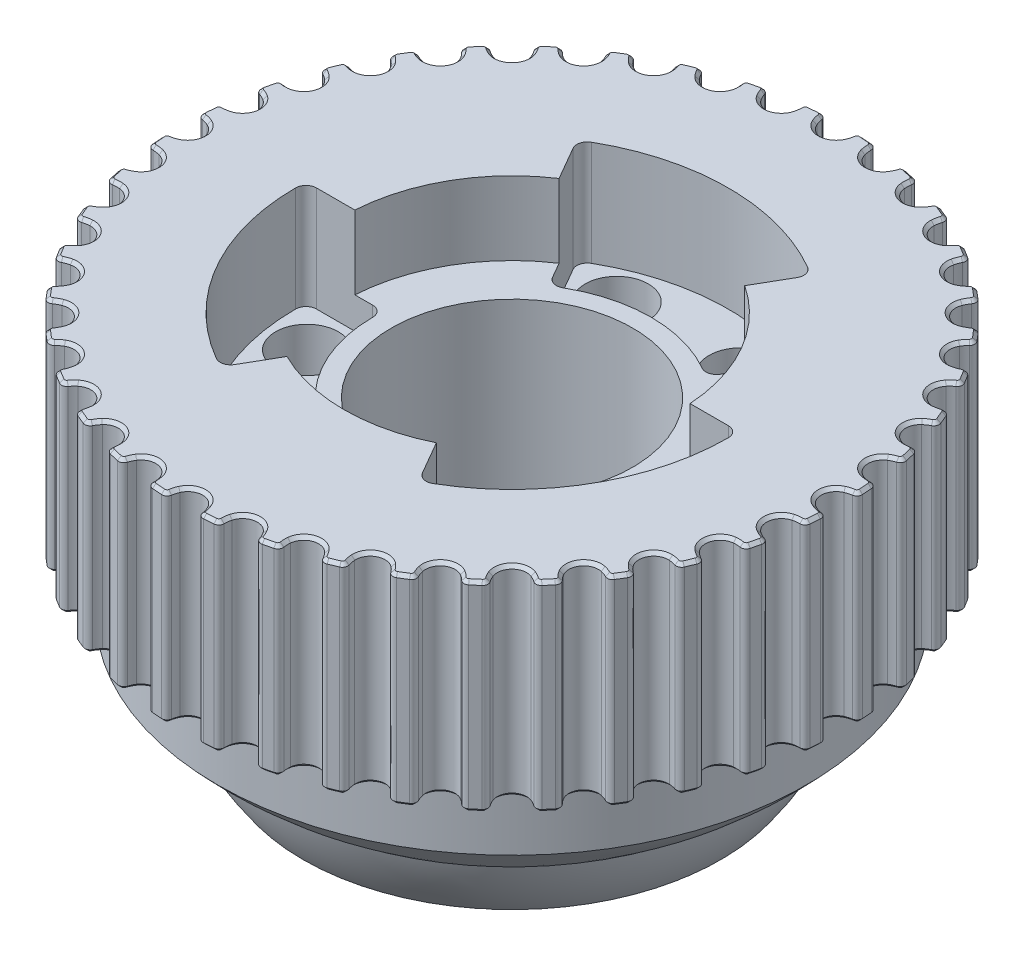
SolidWorks part; units mm, degrees
ref_plane "Front Plane" through (0, 0, 0) normal (0, 0, 1) x (1, 0, 0)
ref_plane "Top Plane" through (0, 0, 0) normal (0, 1, 0) x (1, 0, 0)
ref_plane "Right Plane" through (0, 0, 0) normal (1, 0, 0) x (0, 0, -1)
sketch "Sketch1" plane through (0, 0, 0) normal (0, 1, 0) x (1, 0, 0)
  line L0 (-2.9194, 31.3274) -> (-2.0172, 31.3984)
  line L1 (0, 0) -> (0, 30.8888) construction
  line L2 (0, 0) -> (-4.8321, 30.5085) construction
  line L3 (2.0172, 31.3984) -> (2.9194, 31.3274)
  line L4 (6.9042, 30.6963) -> (7.7841, 30.485)
  line L5 (11.6211, 29.2383) -> (12.4572, 28.892)
  line L6 (16.0519, 27.0604) -> (16.8235, 26.5875)
  line L7 (20.0875, 24.2161) -> (20.7756, 23.6284)
  line L8 (23.6284, 20.7756) -> (24.2161, 20.0875)
  line L9 (26.5875, 16.8235) -> (27.0604, 16.0519)
  line L10 (28.892, 12.4572) -> (29.2383, 11.6211)
  line L11 (30.485, 7.7841) -> (30.6963, 6.9042)
  line L12 (31.3274, 2.9194) -> (31.3984, 2.0172)
  line L13 (31.3984, -2.0172) -> (31.3274, -2.9194)
  line L14 (30.6963, -6.9042) -> (30.485, -7.7841)
  line L15 (29.2383, -11.6211) -> (28.892, -12.4572)
  line L16 (27.0604, -16.0519) -> (26.5875, -16.8235)
  line L17 (24.2161, -20.0875) -> (23.6284, -20.7756)
  line L18 (20.7756, -23.6284) -> (20.0875, -24.2161)
  line L19 (16.8235, -26.5875) -> (16.0519, -27.0604)
  line L20 (12.4572, -28.892) -> (11.6211, -29.2383)
  line L21 (7.7841, -30.485) -> (6.9042, -30.6963)
  line L22 (2.9194, -31.3274) -> (2.0172, -31.3984)
  line L23 (-2.0172, -31.3984) -> (-2.9194, -31.3274)
  line L24 (-6.9042, -30.6963) -> (-7.7841, -30.485)
  line L25 (-11.6211, -29.2383) -> (-12.4572, -28.892)
  line L26 (-16.0519, -27.0604) -> (-16.8235, -26.5875)
  line L27 (-20.0875, -24.2161) -> (-20.7756, -23.6284)
  line L28 (-23.6284, -20.7756) -> (-24.2161, -20.0875)
  line L29 (-26.5875, -16.8235) -> (-27.0604, -16.0519)
  line L30 (-28.892, -12.4572) -> (-29.2383, -11.6211)
  line L31 (-30.485, -7.7841) -> (-30.6963, -6.9042)
  line L32 (-31.3274, -2.9194) -> (-31.3984, -2.0172)
  line L33 (-31.3984, 2.0172) -> (-31.3274, 2.9194)
  line L34 (-30.6963, 6.9042) -> (-30.485, 7.7841)
  line L35 (-29.2383, 11.6211) -> (-28.892, 12.4572)
  line L36 (-27.0604, 16.0519) -> (-26.5875, 16.8235)
  line L37 (-24.2161, 20.0875) -> (-23.6284, 20.7756)
  line L38 (-20.7756, 23.6284) -> (-20.0875, 24.2161)
  line L39 (-16.8235, 26.5875) -> (-16.0519, 27.0604)
  line L40 (-12.4572, 28.892) -> (-11.6211, 29.2383)
  line L41 (-7.7841, 30.485) -> (-6.9042, 30.6963)
  line L42 (0, 0) -> (1.2885, 30.3296) construction
  arc A0 (-2.0172, 31.3984) -> (-1.4757, 30.9718) centre (-1.9774, 30.892) cw
  arc A1 (-1.4757, 30.9718) -> (-1.2885, 30.3296) centre (1.1557, 31.3903) ccw
  arc A2 (-1.2885, 30.3296) -> (1.2885, 30.3296) centre (0, 30.8888) ccw
  arc A3 (1.4757, 30.9718) -> (1.2885, 30.3296) centre (-1.1557, 31.3903) cw
  arc A4 (2.0172, 31.3984) -> (1.4757, 30.9718) centre (1.9774, 30.892) ccw
  arc A5 (0, 30.8888) -> (-4.8321, 30.5085) centre (0, 0) ccw construction
  arc A6 (2.9194, 31.3274) -> (3.3875, 30.8213) centre (2.8795, 30.821) cw
  arc A7 (3.3875, 30.8213) -> (3.4719, 30.1578) centre (6.052, 30.8231) ccw
  arc A8 (3.4719, 30.1578) -> (6.0172, 29.7546) centre (4.8321, 30.5085) ccw
  arc A9 (6.3026, 30.3596) -> (6.0172, 29.7546) centre (3.7691, 31.1847) cw
  arc A10 (6.9042, 30.6963) -> (6.3026, 30.3596) centre (6.7856, 30.2023) ccw
  arc A11 (7.7841, 30.485) -> (8.1674, 29.9119) centre (7.6656, 29.9911) cw
  arc A12 (8.1674, 29.9119) -> (8.1469, 29.2433) centre (10.7993, 29.4969) ccw
  arc A13 (8.1469, 29.2433) -> (10.5978, 28.447) centre (9.5452, 29.377) ccw
  arc A14 (10.9743, 28.9999) -> (10.5978, 28.447) centre (8.601, 30.2111) cw
  arc A15 (11.6211, 29.2383) -> (10.9743, 28.9999) centre (11.4267, 28.769) ccw
  arc A16 (12.4572, 28.892) -> (12.7461, 28.266) centre (12.2628, 28.4227) cw
  arc A17 (12.7461, 28.266) -> (12.6213, 27.6088) centre (15.2807, 27.4443) ccw
  arc A18 (12.6213, 27.6088) -> (14.9174, 26.4389) centre (14.0232, 27.5221) ccw
  arc A19 (15.3757, 26.9261) -> (14.9174, 26.4389) centre (13.2212, 28.4937) cw
  arc A20 (16.0519, 27.0604) -> (15.3757, 26.9261) centre (15.7865, 26.6272) ccw
  arc A21 (16.8235, 26.5875) -> (17.0109, 25.9241) centre (16.5581, 26.1544) cw
  arc A22 (17.0109, 25.9241) -> (16.7849, 25.2945) centre (19.3858, 24.716) ccw
  arc A23 (16.7849, 25.2945) -> (18.8697, 23.7798) centre (18.156, 24.9896) ccw
  arc A24 (19.3986, 24.1893) -> (18.8697, 23.7798) centre (17.5158, 26.0746) cw
  arc A25 (20.0875, 24.2161) -> (19.3986, 24.1893) centre (19.7576, 23.8299) ccw
  arc A26 (20.7756, 23.6284) -> (20.8569, 22.9438) centre (20.4457, 23.2421) cw
  arc A27 (20.8569, 22.9438) -> (20.5352, 22.3574) centre (23.0135, 21.3791) ccw
  arc A28 (20.5352, 22.3574) -> (22.3574, 20.5352) centre (21.8417, 21.8417) ccw
  arc A29 (22.9438, 20.8569) -> (22.3574, 20.5352) centre (21.3791, 23.0135) cw
  arc A30 (23.6284, 20.7756) -> (22.9438, 20.8569) centre (23.2421, 20.4457) ccw
  arc A31 (24.2161, 20.0875) -> (24.1893, 19.3986) centre (23.8299, 19.7576) cw
  arc A32 (24.1893, 19.3986) -> (23.7798, 18.8697) centre (26.0746, 17.5158) ccw
  arc A33 (23.7798, 18.8697) -> (25.2945, 16.7849) centre (24.9896, 18.156) ccw
  arc A34 (25.9241, 17.0109) -> (25.2945, 16.7849) centre (24.716, 19.3858) cw
  arc A35 (26.5875, 16.8235) -> (25.9241, 17.0109) centre (26.1544, 16.5581) ccw
  arc A36 (27.0604, 16.0519) -> (26.9261, 15.3757) centre (26.6272, 15.7865) cw
  arc A37 (26.9261, 15.3757) -> (26.4389, 14.9174) centre (28.4937, 13.2212) ccw
  arc A38 (26.4389, 14.9174) -> (27.6088, 12.6213) centre (27.5221, 14.0232) ccw
  arc A39 (28.266, 12.7461) -> (27.6088, 12.6213) centre (27.4443, 15.2807) cw
  arc A40 (28.892, 12.4572) -> (28.266, 12.7461) centre (28.4227, 12.2628) ccw
  arc A41 (29.2383, 11.6211) -> (28.9999, 10.9743) centre (28.769, 11.4267) cw
  arc A42 (28.9999, 10.9743) -> (28.447, 10.5978) centre (30.2111, 8.601) ccw
  arc A43 (28.447, 10.5978) -> (29.2433, 8.1469) centre (29.377, 9.5452) ccw
  arc A44 (29.9119, 8.1674) -> (29.2433, 8.1469) centre (29.4969, 10.7993) cw
  arc A45 (30.485, 7.7841) -> (29.9119, 8.1674) centre (29.9911, 7.6656) ccw
  arc A46 (30.6963, 6.9042) -> (30.3596, 6.3026) centre (30.2023, 6.7856) cw
  arc A47 (30.3596, 6.3026) -> (29.7546, 6.0172) centre (31.1847, 3.7691) ccw
  arc A48 (29.7546, 6.0172) -> (30.1578, 3.4719) centre (30.5085, 4.8321) ccw
  arc A49 (30.8213, 3.3875) -> (30.1578, 3.4719) centre (30.8231, 6.052) cw
  arc A50 (31.3274, 2.9194) -> (30.8213, 3.3875) centre (30.821, 2.8795) ccw
  arc A51 (31.3984, 2.0172) -> (30.9718, 1.4757) centre (30.892, 1.9774) cw
  arc A52 (30.9718, 1.4757) -> (30.3296, 1.2885) centre (31.3903, -1.1557) ccw
  arc A53 (30.3296, 1.2885) -> (30.3296, -1.2885) centre (30.8888, 0) ccw
  arc A54 (30.9718, -1.4757) -> (30.3296, -1.2885) centre (31.3903, 1.1557) cw
  arc A55 (31.3984, -2.0172) -> (30.9718, -1.4757) centre (30.892, -1.9774) ccw
  arc A56 (31.3274, -2.9194) -> (30.8213, -3.3875) centre (30.821, -2.8795) cw
  arc A57 (30.8213, -3.3875) -> (30.1578, -3.4719) centre (30.8231, -6.052) ccw
  arc A58 (30.1578, -3.4719) -> (29.7546, -6.0172) centre (30.5085, -4.8321) ccw
  arc A59 (30.3596, -6.3026) -> (29.7546, -6.0172) centre (31.1847, -3.7691) cw
  arc A60 (30.6963, -6.9042) -> (30.3596, -6.3026) centre (30.2023, -6.7856) ccw
  arc A61 (30.485, -7.7841) -> (29.9119, -8.1674) centre (29.9911, -7.6656) cw
  arc A62 (29.9119, -8.1674) -> (29.2433, -8.1469) centre (29.4969, -10.7993) ccw
  arc A63 (29.2433, -8.1469) -> (28.447, -10.5978) centre (29.377, -9.5452) ccw
  arc A64 (28.9999, -10.9743) -> (28.447, -10.5978) centre (30.2111, -8.601) cw
  arc A65 (29.2383, -11.6211) -> (28.9999, -10.9743) centre (28.769, -11.4267) ccw
  arc A66 (28.892, -12.4572) -> (28.266, -12.7461) centre (28.4227, -12.2628) cw
  arc A67 (28.266, -12.7461) -> (27.6088, -12.6213) centre (27.4443, -15.2807) ccw
  arc A68 (27.6088, -12.6213) -> (26.4389, -14.9174) centre (27.5221, -14.0232) ccw
  arc A69 (26.9261, -15.3757) -> (26.4389, -14.9174) centre (28.4937, -13.2212) cw
  arc A70 (27.0604, -16.0519) -> (26.9261, -15.3757) centre (26.6272, -15.7865) ccw
  arc A71 (26.5875, -16.8235) -> (25.9241, -17.0109) centre (26.1544, -16.5581) cw
  arc A72 (25.9241, -17.0109) -> (25.2945, -16.7849) centre (24.716, -19.3858) ccw
  arc A73 (25.2945, -16.7849) -> (23.7798, -18.8697) centre (24.9896, -18.156) ccw
  arc A74 (24.1893, -19.3986) -> (23.7798, -18.8697) centre (26.0746, -17.5158) cw
  arc A75 (24.2161, -20.0875) -> (24.1893, -19.3986) centre (23.8299, -19.7576) ccw
  arc A76 (23.6284, -20.7756) -> (22.9438, -20.8569) centre (23.2421, -20.4457) cw
  arc A77 (22.9438, -20.8569) -> (22.3574, -20.5352) centre (21.3791, -23.0135) ccw
  arc A78 (22.3574, -20.5352) -> (20.5352, -22.3574) centre (21.8417, -21.8417) ccw
  arc A79 (20.8569, -22.9438) -> (20.5352, -22.3574) centre (23.0135, -21.3791) cw
  arc A80 (20.7756, -23.6284) -> (20.8569, -22.9438) centre (20.4457, -23.2421) ccw
  arc A81 (20.0875, -24.2161) -> (19.3986, -24.1893) centre (19.7576, -23.8299) cw
  arc A82 (19.3986, -24.1893) -> (18.8697, -23.7798) centre (17.5158, -26.0746) ccw
  arc A83 (18.8697, -23.7798) -> (16.7849, -25.2945) centre (18.156, -24.9896) ccw
  arc A84 (17.0109, -25.9241) -> (16.7849, -25.2945) centre (19.3858, -24.716) cw
  arc A85 (16.8235, -26.5875) -> (17.0109, -25.9241) centre (16.5581, -26.1544) ccw
  arc A86 (16.0519, -27.0604) -> (15.3757, -26.9261) centre (15.7865, -26.6272) cw
  arc A87 (15.3757, -26.9261) -> (14.9174, -26.4389) centre (13.2212, -28.4937) ccw
  arc A88 (14.9174, -26.4389) -> (12.6213, -27.6088) centre (14.0232, -27.5221) ccw
  arc A89 (12.7461, -28.266) -> (12.6213, -27.6088) centre (15.2807, -27.4443) cw
  arc A90 (12.4572, -28.892) -> (12.7461, -28.266) centre (12.2628, -28.4227) ccw
  arc A91 (11.6211, -29.2383) -> (10.9743, -28.9999) centre (11.4267, -28.769) cw
  arc A92 (10.9743, -28.9999) -> (10.5978, -28.447) centre (8.601, -30.2111) ccw
  arc A93 (10.5978, -28.447) -> (8.1469, -29.2433) centre (9.5452, -29.377) ccw
  arc A94 (8.1674, -29.9119) -> (8.1469, -29.2433) centre (10.7993, -29.4969) cw
  arc A95 (7.7841, -30.485) -> (8.1674, -29.9119) centre (7.6656, -29.9911) ccw
  arc A96 (6.9042, -30.6963) -> (6.3026, -30.3596) centre (6.7856, -30.2023) cw
  arc A97 (6.3026, -30.3596) -> (6.0172, -29.7546) centre (3.7691, -31.1847) ccw
  arc A98 (6.0172, -29.7546) -> (3.4719, -30.1578) centre (4.8321, -30.5085) ccw
  arc A99 (3.3875, -30.8213) -> (3.4719, -30.1578) centre (6.052, -30.8231) cw
  arc A100 (2.9194, -31.3274) -> (3.3875, -30.8213) centre (2.8795, -30.821) ccw
  arc A101 (2.0172, -31.3984) -> (1.4757, -30.9718) centre (1.9774, -30.892) cw
  arc A102 (1.4757, -30.9718) -> (1.2885, -30.3296) centre (-1.1557, -31.3903) ccw
  arc A103 (1.2885, -30.3296) -> (-1.2885, -30.3296) centre (0, -30.8888) ccw
  arc A104 (-1.4757, -30.9718) -> (-1.2885, -30.3296) centre (1.1557, -31.3903) cw
  arc A105 (-2.0172, -31.3984) -> (-1.4757, -30.9718) centre (-1.9774, -30.892) ccw
  arc A106 (-2.9194, -31.3274) -> (-3.3875, -30.8213) centre (-2.8795, -30.821) cw
  arc A107 (-3.3875, -30.8213) -> (-3.4719, -30.1578) centre (-6.052, -30.8231) ccw
  arc A108 (-3.4719, -30.1578) -> (-6.0172, -29.7546) centre (-4.8321, -30.5085) ccw
  arc A109 (-6.3026, -30.3596) -> (-6.0172, -29.7546) centre (-3.7691, -31.1847) cw
  arc A110 (-6.9042, -30.6963) -> (-6.3026, -30.3596) centre (-6.7856, -30.2023) ccw
  arc A111 (-7.7841, -30.485) -> (-8.1674, -29.9119) centre (-7.6656, -29.9911) cw
  arc A112 (-8.1674, -29.9119) -> (-8.1469, -29.2433) centre (-10.7993, -29.4969) ccw
  arc A113 (-8.1469, -29.2433) -> (-10.5978, -28.447) centre (-9.5452, -29.377) ccw
  arc A114 (-10.9743, -28.9999) -> (-10.5978, -28.447) centre (-8.601, -30.2111) cw
  arc A115 (-11.6211, -29.2383) -> (-10.9743, -28.9999) centre (-11.4267, -28.769) ccw
  arc A116 (-12.4572, -28.892) -> (-12.7461, -28.266) centre (-12.2628, -28.4227) cw
  arc A117 (-12.7461, -28.266) -> (-12.6213, -27.6088) centre (-15.2807, -27.4443) ccw
  arc A118 (-12.6213, -27.6088) -> (-14.9174, -26.4389) centre (-14.0232, -27.5221) ccw
  arc A119 (-15.3757, -26.9261) -> (-14.9174, -26.4389) centre (-13.2212, -28.4937) cw
  arc A120 (-16.0519, -27.0604) -> (-15.3757, -26.9261) centre (-15.7865, -26.6272) ccw
  arc A121 (-16.8235, -26.5875) -> (-17.0109, -25.9241) centre (-16.5581, -26.1544) cw
  arc A122 (-17.0109, -25.9241) -> (-16.7849, -25.2945) centre (-19.3858, -24.716) ccw
  arc A123 (-16.7849, -25.2945) -> (-18.8697, -23.7798) centre (-18.156, -24.9896) ccw
  arc A124 (-19.3986, -24.1893) -> (-18.8697, -23.7798) centre (-17.5158, -26.0746) cw
  arc A125 (-20.0875, -24.2161) -> (-19.3986, -24.1893) centre (-19.7576, -23.8299) ccw
  arc A126 (-20.7756, -23.6284) -> (-20.8569, -22.9438) centre (-20.4457, -23.2421) cw
  arc A127 (-20.8569, -22.9438) -> (-20.5352, -22.3574) centre (-23.0135, -21.3791) ccw
  arc A128 (-20.5352, -22.3574) -> (-22.3574, -20.5352) centre (-21.8417, -21.8417) ccw
  arc A129 (-22.9438, -20.8569) -> (-22.3574, -20.5352) centre (-21.3791, -23.0135) cw
  arc A130 (-23.6284, -20.7756) -> (-22.9438, -20.8569) centre (-23.2421, -20.4457) ccw
  arc A131 (-24.2161, -20.0875) -> (-24.1893, -19.3986) centre (-23.8299, -19.7576) cw
  arc A132 (-24.1893, -19.3986) -> (-23.7798, -18.8697) centre (-26.0746, -17.5158) ccw
  arc A133 (-23.7798, -18.8697) -> (-25.2945, -16.7849) centre (-24.9896, -18.156) ccw
  arc A134 (-25.9241, -17.0109) -> (-25.2945, -16.7849) centre (-24.716, -19.3858) cw
  arc A135 (-26.5875, -16.8235) -> (-25.9241, -17.0109) centre (-26.1544, -16.5581) ccw
  arc A136 (-27.0604, -16.0519) -> (-26.9261, -15.3757) centre (-26.6272, -15.7865) cw
  arc A137 (-26.9261, -15.3757) -> (-26.4389, -14.9174) centre (-28.4937, -13.2212) ccw
  arc A138 (-26.4389, -14.9174) -> (-27.6088, -12.6213) centre (-27.5221, -14.0232) ccw
  arc A139 (-28.266, -12.7461) -> (-27.6088, -12.6213) centre (-27.4443, -15.2807) cw
  arc A140 (-28.892, -12.4572) -> (-28.266, -12.7461) centre (-28.4227, -12.2628) ccw
  arc A141 (-29.2383, -11.6211) -> (-28.9999, -10.9743) centre (-28.769, -11.4267) cw
  arc A142 (-28.9999, -10.9743) -> (-28.447, -10.5978) centre (-30.2111, -8.601) ccw
  arc A143 (-28.447, -10.5978) -> (-29.2433, -8.1469) centre (-29.377, -9.5452) ccw
  arc A144 (-29.9119, -8.1674) -> (-29.2433, -8.1469) centre (-29.4969, -10.7993) cw
  arc A145 (-30.485, -7.7841) -> (-29.9119, -8.1674) centre (-29.9911, -7.6656) ccw
  arc A146 (-30.6963, -6.9042) -> (-30.3596, -6.3026) centre (-30.2023, -6.7856) cw
  arc A147 (-30.3596, -6.3026) -> (-29.7546, -6.0172) centre (-31.1847, -3.7691) ccw
  arc A148 (-29.7546, -6.0172) -> (-30.1578, -3.4719) centre (-30.5085, -4.8321) ccw
  arc A149 (-30.8213, -3.3875) -> (-30.1578, -3.4719) centre (-30.8231, -6.052) cw
  arc A150 (-31.3274, -2.9194) -> (-30.8213, -3.3875) centre (-30.821, -2.8795) ccw
  arc A151 (-31.3984, -2.0172) -> (-30.9718, -1.4757) centre (-30.892, -1.9774) cw
  arc A152 (-30.9718, -1.4757) -> (-30.3296, -1.2885) centre (-31.3903, 1.1557) ccw
  arc A153 (-30.3296, -1.2885) -> (-30.3296, 1.2885) centre (-30.8888, 0) ccw
  arc A154 (-30.9718, 1.4757) -> (-30.3296, 1.2885) centre (-31.3903, -1.1557) cw
  arc A155 (-31.3984, 2.0172) -> (-30.9718, 1.4757) centre (-30.892, 1.9774) ccw
  arc A156 (-31.3274, 2.9194) -> (-30.8213, 3.3875) centre (-30.821, 2.8795) cw
  arc A157 (-30.8213, 3.3875) -> (-30.1578, 3.4719) centre (-30.8231, 6.052) ccw
  arc A158 (-30.1578, 3.4719) -> (-29.7546, 6.0172) centre (-30.5085, 4.8321) ccw
  arc A159 (-30.3596, 6.3026) -> (-29.7546, 6.0172) centre (-31.1847, 3.7691) cw
  arc A160 (-30.6963, 6.9042) -> (-30.3596, 6.3026) centre (-30.2023, 6.7856) ccw
  arc A161 (-30.485, 7.7841) -> (-29.9119, 8.1674) centre (-29.9911, 7.6656) cw
  arc A162 (-29.9119, 8.1674) -> (-29.2433, 8.1469) centre (-29.4969, 10.7993) ccw
  arc A163 (-29.2433, 8.1469) -> (-28.447, 10.5978) centre (-29.377, 9.5452) ccw
  arc A164 (-28.9999, 10.9743) -> (-28.447, 10.5978) centre (-30.2111, 8.601) cw
  arc A165 (-29.2383, 11.6211) -> (-28.9999, 10.9743) centre (-28.769, 11.4267) ccw
  arc A166 (-28.892, 12.4572) -> (-28.266, 12.7461) centre (-28.4227, 12.2628) cw
  arc A167 (-28.266, 12.7461) -> (-27.6088, 12.6213) centre (-27.4443, 15.2807) ccw
  arc A168 (-27.6088, 12.6213) -> (-26.4389, 14.9174) centre (-27.5221, 14.0232) ccw
  arc A169 (-26.9261, 15.3757) -> (-26.4389, 14.9174) centre (-28.4937, 13.2212) cw
  arc A170 (-27.0604, 16.0519) -> (-26.9261, 15.3757) centre (-26.6272, 15.7865) ccw
  arc A171 (-26.5875, 16.8235) -> (-25.9241, 17.0109) centre (-26.1544, 16.5581) cw
  arc A172 (-25.9241, 17.0109) -> (-25.2945, 16.7849) centre (-24.716, 19.3858) ccw
  arc A173 (-25.2945, 16.7849) -> (-23.7798, 18.8697) centre (-24.9896, 18.156) ccw
  arc A174 (-24.1893, 19.3986) -> (-23.7798, 18.8697) centre (-26.0746, 17.5158) cw
  arc A175 (-24.2161, 20.0875) -> (-24.1893, 19.3986) centre (-23.8299, 19.7576) ccw
  arc A176 (-23.6284, 20.7756) -> (-22.9438, 20.8569) centre (-23.2421, 20.4457) cw
  arc A177 (-22.9438, 20.8569) -> (-22.3574, 20.5352) centre (-21.3791, 23.0135) ccw
  arc A178 (-22.3574, 20.5352) -> (-20.5352, 22.3574) centre (-21.8417, 21.8417) ccw
  arc A179 (-20.8569, 22.9438) -> (-20.5352, 22.3574) centre (-23.0135, 21.3791) cw
  arc A180 (-20.7756, 23.6284) -> (-20.8569, 22.9438) centre (-20.4457, 23.2421) ccw
  arc A181 (-20.0875, 24.2161) -> (-19.3986, 24.1893) centre (-19.7576, 23.8299) cw
  arc A182 (-19.3986, 24.1893) -> (-18.8697, 23.7798) centre (-17.5158, 26.0746) ccw
  arc A183 (-18.8697, 23.7798) -> (-16.7849, 25.2945) centre (-18.156, 24.9896) ccw
  arc A184 (-17.0109, 25.9241) -> (-16.7849, 25.2945) centre (-19.3858, 24.716) cw
  arc A185 (-16.8235, 26.5875) -> (-17.0109, 25.9241) centre (-16.5581, 26.1544) ccw
  arc A186 (-16.0519, 27.0604) -> (-15.3757, 26.9261) centre (-15.7865, 26.6272) cw
  arc A187 (-15.3757, 26.9261) -> (-14.9174, 26.4389) centre (-13.2212, 28.4937) ccw
  arc A188 (-14.9174, 26.4389) -> (-12.6213, 27.6088) centre (-14.0232, 27.5221) ccw
  arc A189 (-12.7461, 28.266) -> (-12.6213, 27.6088) centre (-15.2807, 27.4443) cw
  arc A190 (-12.4572, 28.892) -> (-12.7461, 28.266) centre (-12.2628, 28.4227) ccw
  arc A191 (-11.6211, 29.2383) -> (-10.9743, 28.9999) centre (-11.4267, 28.769) cw
  arc A192 (-10.9743, 28.9999) -> (-10.5978, 28.447) centre (-8.601, 30.2111) ccw
  arc A193 (-10.5978, 28.447) -> (-8.1469, 29.2433) centre (-9.5452, 29.377) ccw
  arc A194 (-8.1674, 29.9119) -> (-8.1469, 29.2433) centre (-10.7993, 29.4969) cw
  arc A195 (-7.7841, 30.485) -> (-8.1674, 29.9119) centre (-7.6656, 29.9911) ccw
  arc A196 (-6.9042, 30.6963) -> (-6.3026, 30.3596) centre (-6.7856, 30.2023) cw
  arc A197 (-6.3026, 30.3596) -> (-6.0172, 29.7546) centre (-3.7691, 31.1847) ccw
  arc A198 (-6.0172, 29.7546) -> (-3.4719, 30.1578) centre (-4.8321, 30.5085) ccw
  arc A199 (-3.3875, 30.8213) -> (-3.4719, 30.1578) centre (-6.052, 30.8231) cw
  arc A200 (-2.9194, 31.3274) -> (-3.3875, 30.8213) centre (-2.8795, 30.821) ccw
  point P18 (0, 29.4842)
  dimension "D1" = 1.4046
  dimension "D4" = 2.6645
  dimension "D5" = 0.508
  dimension "D7" = 4.852
  dimension "D2" = 1.6312
  dimension "D3" = 0.6707
extrude "Boss-Extrude1" add sketch "Sketch1" along normal blind 19.08 contours A5 A199 A198 A197 A196 L41 A195 A194 A193 A192 A191 L40 A190 A189 A188 A187 A186 L39 A185 A184 A183 A182 A181 L38 A180 A179 A178 A177 A176 L37 A175 A174 A173 A172 A171 L36 A170 A169 A168 A167 A166 L35 A165 A164 A163 A162 A161 L34 A160 A159 A158
sketch "Sketch2" plane through (0, 0, 0) normal (0, 1, 0) x (1, 0, 0)
  circle A0 centre (0, 0) radius 22.6898 construction
chamfer "Chamfer1" distance 0.3 angle 45 480 edges at (-20.4316, 19.08, -23.9223) (-20.9502, 19.08, -23.302) (-20.6775, 19.08, -22.6607) (-20.8485, 19.08, -20.8485) (-22.6607, 19.08, -20.6775) (-23.302, 19.08, -20.9502) (-23.9223, 19.08, -20.4316) (-24.3375, 19.08, -19.7378) (-3.4088, 19.08, -30.4869) (-23.9679, 19.08, -19.1471) (-23.8532, 19.08, -17.3304) (-25.6164, 19.08, -16.8781) (-26.2925, 19.08, -17.047) (-26.824, 19.08, -16.4377) (-27.1255, 19.08, -15.6876) (-26.6681, 19.08, -15.1619) (-26.2706, 19.08, -13.3855) (-27.9414, 19.08, -12.663) (-28.6355, 19.08, -12.7241) (-4.6123, 19.08, -29.1212) (-29.0651, 19.08, -12.0392) (-29.2456, 19.08, -11.2511) (-28.7116, 19.08, -10.8035) (-28.0411, 19.08, -9.1111) (-29.5783, 19.08, -8.1361) (-30.2734, 19.08, -8.0878) (-30.5906, 19.08, -7.3442) (-30.6456, 19.08, -6.5375) (-30.0481, 19.08, -6.179) (-29.1212, 19.08, -4.6123) (-6.179, 19.08, -30.0481) (-30.4869, 19.08, -3.4088) (-31.1659, 19.08, -3.2525) (-1.663, 0, -31.291) (-1.4023, 0, -30.6448) (0, 0, -29.4842) (1.4023, 0, -30.6448) (1.663, 0, -31.291) (2.4683, 0, -31.3629) (3.2525, 0, -31.1659) (-31.3629, 19.08, -2.4683) (3.4088, 0, -30.4869) (4.6123, 0, -29.1212) (6.179, 0, -30.0481) (6.5375, 0, -30.6456) (7.3442, 0, -30.5906) (8.0878, 0, -30.2734) (8.1361, 0, -29.5783) (9.1111, 0, -28.0411) (-31.291, 19.08, -1.663) (10.8035, 0, -28.7116) (11.2511, 0, -29.2456) (12.0392, 0, -29.0651) (12.7241, 0, -28.6355) (12.663, 0, -27.9414) (13.3855, 0, -26.2706) (15.1619, 0, -26.6681) (15.6876, 0, -27.1255) (-30.6448, 19.08, -1.4023) (16.4377, 0, -26.824) (17.047, 0, -26.2925) (16.8781, 0, -25.6164) (17.3304, 0, -23.8532) (19.1471, 0, -23.9679) (19.7378, 0, -24.3375) (20.4316, 0, -23.9223) (20.9502, 0, -23.302) (-29.4842, 19.08, 0) (20.6775, 0, -22.6607) (20.8485, 0, -20.8485) (22.6607, 0, -20.6775) (23.302, 0, -20.9502) (23.9223, 0, -20.4316) (24.3375, 0, -19.7378) (23.9679, 0, -19.1471) (23.8532, 0, -17.3304) (-30.6448, 19.08, 1.4023) (25.6164, 0, -16.8781) (26.2925, 0, -17.047) (26.824, 0, -16.4377) (27.1255, 0, -15.6876) (26.6681, 0, -15.1619) (26.2706, 0, -13.3855) (27.9414, 0, -12.663) (28.6355, 0, -12.7241) (-31.291, 19.08, 1.663) (29.0651, 0, -12.0392) (29.2456, 0, -11.2511) (28.7116, 0, -10.8035) (28.0411, 0, -9.1111) (29.5783, 0, -8.1361) (30.2734, 0, -8.0878) (30.5906, 0, -7.3442) (30.6456, 0, -6.5375) (-31.3629, 19.08, 2.4683) (30.0481, 0, -6.179) (29.1212, 0, -4.6123) (30.4869, 0, -3.4088) (31.1659, 0, -3.2525) (31.3629, 0, -2.4683) (31.291, 0, -1.663) (30.6448, 0, -1.4023) (29.4842, 0, 0) (-31.1659, 19.08, 3.2525) (30.6448, 0, 1.4023) (31.291, 0, 1.663) (-6.5375, 19.08, -30.6456) (31.3629, 0, 2.4683) (31.1659, 0, 3.2525) (30.4869, 0, 3.4088) (29.1212, 0, 4.6123) (30.0481, 0, 6.179) (30.6456, 0, 6.5375) (-30.4869, 19.08, 3.4088) (30.5906, 0, 7.3442) (30.2734, 0, 8.0878) (29.5783, 0, 8.1361) (28.0411, 0, 9.1111) (28.7116, 0, 10.8035) (29.2456, 0, 11.2511) (29.0651, 0, 12.0392) (28.6355, 0, 12.7241) (-29.1212, 19.08, 4.6123) (27.9414, 0, 12.663) (26.2706, 0, 13.3855) (26.6681, 0, 15.1619) (27.1255, 0, 15.6876) (26.824, 0, 16.4377) (26.2925, 0, 17.047) (25.6164, 0, 16.8781) (23.8532, 0, 17.3304) (-30.0481, 19.08, 6.179) (23.9679, 0, 19.1471) (24.3375, 0, 19.7378) (23.9223, 0, 20.4316) (23.302, 0, 20.9502) (22.6607, 0, 20.6775) (20.8485, 0, 20.8485) (20.6775, 0, 22.6607) (20.9502, 0, 23.302) (-30.6456, 19.08, 6.5375) (20.4316, 0, 23.9223) (19.7378, 0, 24.3375) (19.1471, 0, 23.9679) (17.3304, 0, 23.8532) (16.8781, 0, 25.6164) (17.047, 0, 26.2925) (16.4377, 0, 26.824) (15.6876, 0, 27.1255) (-30.5906, 19.08, 7.3442) (15.1619, 0, 26.6681) (13.3855, 0, 26.2706) (12.663, 0, 27.9414) (12.7241, 0, 28.6355) (12.0392, 0, 29.0651) (11.2511, 0, 29.2456) (10.8035, 0, 28.7116) (9.1111, 0, 28.0411) (-30.2734, 19.08, 8.0878) (8.1361, 0, 29.5783) (8.0878, 0, 30.2734) (7.3442, 0, 30.5906) (6.5375, 0, 30.6456) (6.179, 0, 30.0481) (4.6123, 0, 29.1212) (3.4088, 0, 30.4869) (3.2525, 0, 31.1659) (-29.5783, 19.08, 8.1361) (2.4683, 0, 31.3629) (1.663, 0, 31.291) (1.4023, 0, 30.6448) (0, 0, 29.4842) (-1.4023, 0, 30.6448) (-1.663, 0, 31.291) (-2.4683, 0, 31.3629) (-3.2525, 0, 31.1659) (-28.0411, 19.08, 9.1111) (-3.4088, 0, 30.4869) (-4.6123, 0, 29.1212) (-6.179, 0, 30.0481) (-6.5375, 0, 30.6456) (-7.3442, 0, 30.5906) (-8.0878, 0, 30.2734) (-8.1361, 0, 29.5783) (-9.1111, 0, 28.0411) (-28.7116, 19.08, 10.8035) (-10.8035, 0, 28.7116) (-11.2511, 0, 29.2456) (-12.0392, 0, 29.0651) (-12.7241, 0, 28.6355) (-12.663, 0, 27.9414) (-13.3855, 0, 26.2706) (-15.1619, 0, 26.6681) (-15.6876, 0, 27.1255) (-29.2456, 19.08, 11.2511) (-16.4377, 0, 26.824) (-17.047, 0, 26.2925) (-7.3442, 19.08, -30.5906) (-16.8781, 0, 25.6164) (-17.3304, 0, 23.8532) (-19.1471, 0, 23.9679) (-19.7378, 0, 24.3375) (-20.4316, 0, 23.9223) (-20.9502, 0, 23.302) (-29.0651, 19.08, 12.0392) (-20.6775, 0, 22.6607) (-20.8485, 0, 20.8485) (-22.6607, 0, 20.6775) (-23.302, 0, 20.9502) (-23.9223, 0, 20.4316) (-24.3375, 0, 19.7378) (-23.9679, 0, 19.1471) (-23.8532, 0, 17.3304) (-28.6355, 19.08, 12.7241) (-25.6164, 0, 16.8781) (-26.2925, 0, 17.047) (-26.824, 0, 16.4377) (-27.1255, 0, 15.6876) (-26.6681, 0, 15.1619) (-26.2706, 0, 13.3855) (-27.9414, 0, 12.663) (-28.6355, 0, 12.7241) (-27.9414, 19.08, 12.663) (-29.0651, 0, 12.0392) (-29.2456, 0, 11.2511) (-28.7116, 0, 10.8035) (-28.0411, 0, 9.1111) (-29.5783, 0, 8.1361) (-30.2734, 0, 8.0878) (-30.5906, 0, 7.3442) (-30.6456, 0, 6.5375) (-26.2706, 19.08, 13.3855) (-30.0481, 0, 6.179) (-29.1212, 0, 4.6123) (-30.4869, 0, 3.4088) (-31.1659, 0, 3.2525) (-31.3629, 0, 2.4683) (-31.291, 0, 1.663) (-30.6448, 0, 1.4023) (-29.4842, 0, 0) (-26.6681, 19.08, 15.1619) (-30.6448, 0, -1.4023) (-31.291, 0, -1.663) (-31.3629, 0, -2.4683) (-31.1659, 0, -3.2525) (-30.4869, 0, -3.4088) (-29.1212, 0, -4.6123) (-30.0481, 0, -6.179) (-30.6456, 0, -6.5375) (-27.1255, 19.08, 15.6876) (-30.5906, 0, -7.3442) (-30.2734, 0, -8.0878) (-29.5783, 0, -8.1361) (-28.0411, 0, -9.1111) (-28.7116, 0, -10.8035) (-29.2456, 0, -11.2511) (-29.0651, 0, -12.0392) (-28.6355, 0, -12.7241) (-26.824, 19.08, 16.4377) (-27.9414, 0, -12.663) (-26.2706, 0, -13.3855) (-26.6681, 0, -15.1619) (-27.1255, 0, -15.6876) (-26.824, 0, -16.4377) (-26.2925, 0, -17.047) (-25.6164, 0, -16.8781) (-23.8532, 0, -17.3304) (-26.2925, 19.08, 17.047) (-23.9679, 0, -19.1471) (-24.3375, 0, -19.7378) (-23.9223, 0, -20.4316) (-23.302, 0, -20.9502) (-22.6607, 0, -20.6775) (-20.8485, 0, -20.8485) (-20.6775, 0, -22.6607) (-20.9502, 0, -23.302) (-25.6164, 19.08, 16.8781) (-20.4316, 0, -23.9223) (-19.7378, 0, -24.3375) (-19.1471, 0, -23.9679) (-17.3304, 0, -23.8532) (-16.8781, 0, -25.6164) (-17.047, 0, -26.2925) (-16.4377, 0, -26.824) (-15.6876, 0, -27.1255) (-23.8532, 19.08, 17.3304) (-15.1619, 0, -26.6681) (-13.3855, 0, -26.2706) (-8.0878, 19.08, -30.2734) (-12.663, 0, -27.9414) (-12.7241, 0, -28.6355) (-12.0392, 0, -29.0651) (-11.2511, 0, -29.2456) (-10.8035, 0, -28.7116) (-9.1111, 0, -28.0411) (-23.9679, 19.08, 19.1471) (-8.1361, 0, -29.5783) (-8.0878, 0, -30.2734) (-7.3442, 0, -30.5906) (-6.5375, 0, -30.6456) (-6.179, 0, -30.0481) (-4.6123, 0, -29.1212) (-3.4088, 0, -30.4869) (-3.2525, 0, -31.1659) (-24.3375, 19.08, 19.7378) (-2.4683, 0, -31.3629) (-23.9223, 19.08, 20.4316) (-23.302, 19.08, 20.9502) (-22.6607, 19.08, 20.6775) (-20.8485, 19.08, 20.8485) (-20.6775, 19.08, 22.6607) (-20.9502, 19.08, 23.302) (-20.4316, 19.08, 23.9223) (-19.7378, 19.08, 24.3375) (-8.1361, 19.08, -29.5783) (-19.1471, 19.08, 23.9679) (-17.3304, 19.08, 23.8532) (-16.8781, 19.08, 25.6164) (-17.047, 19.08, 26.2925) (-16.4377, 19.08, 26.824) (-15.6876, 19.08, 27.1255) (-15.1619, 19.08, 26.6681) (-13.3855, 19.08, 26.2706) (-12.663, 19.08, 27.9414) (-12.7241, 19.08, 28.6355) (-9.1111, 19.08, -28.0411) (-12.0392, 19.08, 29.0651) (-11.2511, 19.08, 29.2456) (-10.8035, 19.08, 28.7116) (-9.1111, 19.08, 28.0411) (-8.1361, 19.08, 29.5783) (-8.0878, 19.08, 30.2734) (-7.3442, 19.08, 30.5906) (-6.5375, 19.08, 30.6456) (-6.179, 19.08, 30.0481) (-4.6123, 19.08, 29.1212) (-10.8035, 19.08, -28.7116) (-3.4088, 19.08, 30.4869) (-3.2525, 19.08, 31.1659) (-2.4683, 19.08, 31.3629) (-1.663, 19.08, 31.291) (-1.4023, 19.08, 30.6448) (0, 19.08, 29.4842) (1.4023, 19.08, 30.6448) (1.663, 19.08, 31.291) (2.4683, 19.08, 31.3629) (3.2525, 19.08, 31.1659) (-11.2511, 19.08, -29.2456) (3.4088, 19.08, 30.4869) (4.6123, 19.08, 29.1212) (-2.4683, 19.08, -31.3629) (6.179, 19.08, 30.0481) (6.5375, 19.08, 30.6456) (7.3442, 19.08, 30.5906) (8.0878, 19.08, 30.2734) (8.1361, 19.08, 29.5783) (9.1111, 19.08, 28.0411) (10.8035, 19.08, 28.7116) (11.2511, 19.08, 29.2456) (-12.0392, 19.08, -29.0651) (12.0392, 19.08, 29.0651) (12.7241, 19.08, 28.6355) (12.663, 19.08, 27.9414) (13.3855, 19.08, 26.2706) (15.1619, 19.08, 26.6681) (15.6876, 19.08, 27.1255) (16.4377, 19.08, 26.824) (17.047, 19.08, 26.2925) (16.8781, 19.08, 25.6164) (17.3304, 19.08, 23.8532) (-12.7241, 19.08, -28.6355) (19.1471, 19.08, 23.9679) (19.7378, 19.08, 24.3375) (20.4316, 19.08, 23.9223) (20.9502, 19.08, 23.302) (20.6775, 19.08, 22.6607) (20.8485, 19.08, 20.8485) (22.6607, 19.08, 20.6775) (23.302, 19.08, 20.9502) (23.9223, 19.08, 20.4316) (24.3375, 19.08, 19.7378) (-12.663, 19.08, -27.9414) (23.9679, 19.08, 19.1471) (23.8532, 19.08, 17.3304) (25.6164, 19.08, 16.8781) (26.2925, 19.08, 17.047) (26.824, 19.08, 16.4377) (27.1255, 19.08, 15.6876) (26.6681, 19.08, 15.1619) (26.2706, 19.08, 13.3855) (27.9414, 19.08, 12.663) (28.6355, 19.08, 12.7241) (-13.3855, 19.08, -26.2706) (29.0651, 19.08, 12.0392) (29.2456, 19.08, 11.2511) (28.7116, 19.08, 10.8035) (28.0411, 19.08, 9.1111) (29.5783, 19.08, 8.1361) (30.2734, 19.08, 8.0878) (30.5906, 19.08, 7.3442) (30.6456, 19.08, 6.5375) (30.0481, 19.08, 6.179) (29.1212, 19.08, 4.6123) (-15.1619, 19.08, -26.6681) (30.4869, 19.08, 3.4088) (31.1659, 19.08, 3.2525) (31.3629, 19.08, 2.4683) (31.291, 19.08, 1.663) (30.6448, 19.08, 1.4023) (29.4842, 19.08, 0) (30.6448, 19.08, -1.4023) (31.291, 19.08, -1.663) (31.3629, 19.08, -2.4683) (31.1659, 19.08, -3.2525) (-15.6876, 19.08, -27.1255) (30.4869, 19.08, -3.4088) (29.1212, 19.08, -4.6123) (30.0481, 19.08, -6.179) (30.6456, 19.08, -6.5375) (30.5906, 19.08, -7.3442) (30.2734, 19.08, -8.0878) (29.5783, 19.08, -8.1361) (28.0411, 19.08, -9.1111) (28.7116, 19.08, -10.8035) (29.2456, 19.08, -11.2511) (-16.4377, 19.08, -26.824) (29.0651, 19.08, -12.0392) (28.6355, 19.08, -12.7241) (27.9414, 19.08, -12.663) (26.2706, 19.08, -13.3855) (26.6681, 19.08, -15.1619) (27.1255, 19.08, -15.6876) (26.824, 19.08, -16.4377) (26.2925, 19.08, -17.047) (25.6164, 19.08, -16.8781) (23.8532, 19.08, -17.3304) (-17.047, 19.08, -26.2925) (23.9679, 19.08, -19.1471) (24.3375, 19.08, -19.7378) (23.9223, 19.08, -20.4316) (23.302, 19.08, -20.9502) (22.6607, 19.08, -20.6775) (20.8485, 19.08, -20.8485) (20.6775, 19.08, -22.6607) (20.9502, 19.08, -23.302) (20.4316, 19.08, -23.9223) (19.7378, 19.08, -24.3375) (-16.8781, 19.08, -25.6164) (19.1471, 19.08, -23.9679) (17.3304, 19.08, -23.8532) (16.8781, 19.08, -25.6164) (17.047, 19.08, -26.2925) (16.4377, 19.08, -26.824) (15.6876, 19.08, -27.1255) (15.1619, 19.08, -26.6681) (13.3855, 19.08, -26.2706) (12.663, 19.08, -27.9414) (12.7241, 19.08, -28.6355) (-17.3304, 19.08, -23.8532) (12.0392, 19.08, -29.0651) (11.2511, 19.08, -29.2456) (-3.2525, 19.08, -31.1659) (10.8035, 19.08, -28.7116) (9.1111, 19.08, -28.0411) (8.1361, 19.08, -29.5783) (8.0878, 19.08, -30.2734) (7.3442, 19.08, -30.5906) (6.5375, 19.08, -30.6456) (6.179, 19.08, -30.0481) (4.6123, 19.08, -29.1212) (-19.1471, 19.08, -23.9679) (3.4088, 19.08, -30.4869) (3.2525, 19.08, -31.1659) (2.4683, 19.08, -31.3629) (1.663, 19.08, -31.291) (1.4023, 19.08, -30.6448) (0, 19.08, -29.4842) (-1.4023, 19.08, -30.6448) (-1.663, 19.08, -31.291) (-19.7378, 19.08, -24.3375)
sketch "Sketch3" plane through (0, 19.08, 0) normal (0, 1, 0) x (1, 0, 0)
  circle A42 centre (0, 0) radius 16
  dimension "D1" = 32
extrude "Cut-Extrude1" cut sketch "Sketch3" against normal blind 7
sketch "Sketch4" plane through (0, 12.08, 0) normal (0, 1, 0) x (1, 0, 0)
  circle A0 centre (0, 0) radius 11.5
  dimension "D1" = 23
sketch "Sketch7" plane through (0, 0, 0) normal (0, 0, 1) x (1, 0, 0)
  line L0 (28.0643, 0) -> (28.0643, -5.8438)
  line L1 (0, 40.9518) -> (0, -40.2331) construction
  line L2 (19.9085, -16.0962) -> (0, -16.0962)
  line L3 (0, 0) -> (28.0643, 0)
  line L4 (0, 0) -> (0, -16.0962)
  line L5 (22.7634, -10.5531) -> (0, -10.5531) construction
  line L6 (28.0643, -5.8438) -> (0, -5.8438) construction
  arc A0 (28.0643, -5.8438) -> (22.7634, -10.5531) centre (2.9108, 17.1312) cw
  arc A1 (22.7634, -10.5531) -> (19.9085, -16.0962) centre (4.4949, -4.6509) cw
  arc A2 (22, -11) -> (31.5, -3) centre (5.174, 18.6215) ccw construction
  arc A4 (19, -17.4926) -> (22, -11) centre (3.3772, -6.3345) ccw construction
revolve "Revolve2" add sketch "Sketch7" angle 360 about L1
extrude "Cut-Extrude3" cut sketch "Sketch4" against normal through all
sketch "Sketch10" plane through (0, 19.08, 0) normal (0, 1, 0) x (1, 0, 0)
  line L0 (0, 0) -> (0, 26.2988) construction
  circle A1 centre (-5.901, 15.8839) radius 3
  circle A2 centre (5.901, 15.8839) radius 3
  arc A3 (-5.901, 15.8839) -> (0, 16.9447) centre (0, 0) cw construction
  arc A4 (0, 16.9447) -> (5.901, 15.8839) centre (0, 0) cw construction
  circle A5 centre (16.7064, -2.8316) radius 3
  circle A6 centre (10.8054, -13.0524) radius 3
  circle A7 centre (-10.8054, -13.0524) radius 3
  circle A8 centre (-16.7064, -2.8316) radius 3
  point P20 (0, 0)
  dimension "D1" = 6
  dimension "D2" = 3
extrude "Cut-Extrude5" cut sketch "Sketch10" against normal through all
sketch "Sketch11" plane through (0, 19.08, 0) normal (0, 1, 0) x (1, 0, 0)
  line L0 (0, 28.1742) -> (0, 0) construction
  line L1 (1.8222, 20.5402) -> (1.1725, 13.2165) construction
  line L2 (10.6729, 16.4943) -> (7.9967, 11.8589)
  line L3 (-10.6729, 16.4943) -> (-7.9967, 11.8589)
  arc A0 (-6.6309, 11.4927) -> (6.6309, 11.4927) centre (0, 0) cw
  arc A1 (-10.3067, 17.8604) -> (10.3067, 17.8604) centre (0, 0) cw
  circle A2 centre (-5.901, 15.8839) radius 2 construction
  circle A3 centre (5.901, 15.8839) radius 2 construction
  arc A4 (-5.901, 15.8839) -> (5.901, 15.8839) centre (0, 0) cw construction
  arc A5 (7.9967, 11.8589) -> (6.6309, 11.4927) centre (7.1306, 12.3589) cw
  arc A6 (10.3067, 17.8604) -> (10.6729, 16.4943) centre (9.8069, 16.9943) cw
  arc A7 (-10.3067, 17.8604) -> (-10.6729, 16.4943) centre (-9.8069, 16.9943) ccw
  arc A8 (-6.6309, 11.4927) -> (-7.9967, 11.8589) centre (-7.1306, 12.3589) cw
  point P5 (0, 13.2684)
  point P6 (0, 20.6209)
  point P11 (1.4973, 16.8784)
  dimension "D1" = 1
  dimension "D2" = 1
  dimension "D3" = 60
extrude "Cut-Extrude6" cut sketch "Sketch11" against normal blind 10
pattern_circular "CirPattern1" count 3 over 360 about axis through (0, 0, 0) along (0, 1, 0) of "Cut-Extrude6"
